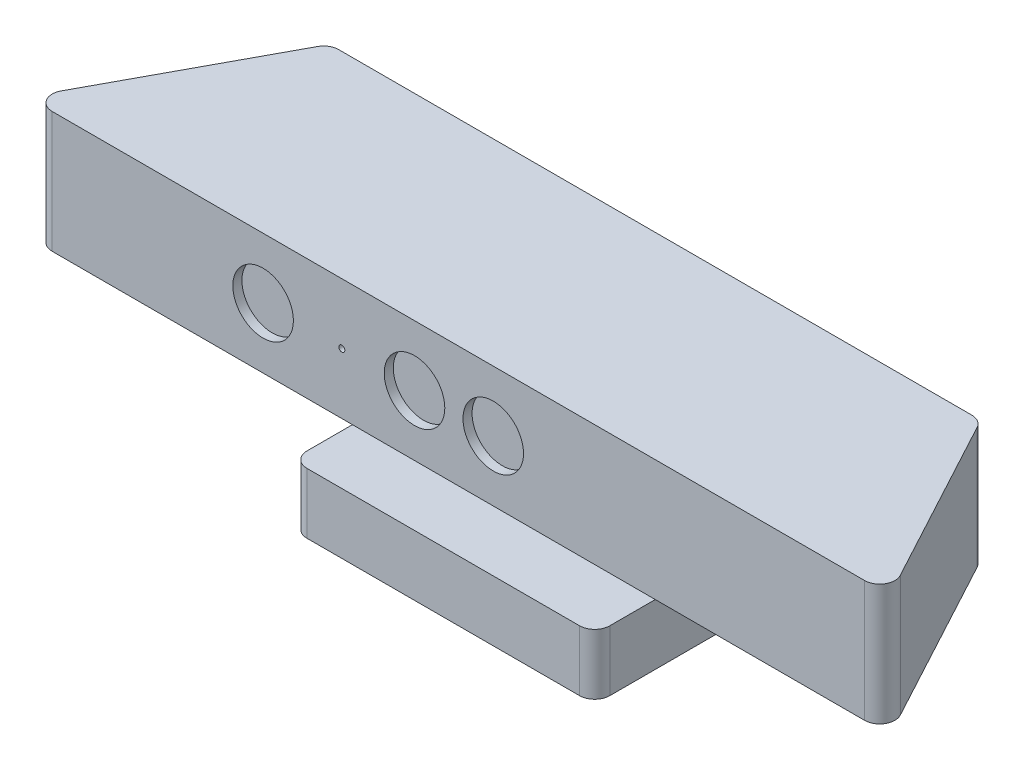
SolidWorks part; units mm, degrees
ref_plane "Front Plane" through (0, 0, 0) normal (0, 0, 1) x (1, 0, 0)
ref_plane "Top Plane" through (0, 0, 0) normal (0, 1, 0) x (1, 0, 0)
ref_plane "Right Plane" through (0, 0, 0) normal (1, 0, 0) x (0, 0, -1)
sketch "Sketch2" plane through (0, 0, 0) normal (0, 1, 0) x (1, 0, 0)
  line L0 (0, -15.7414) -> (0, -80.7414) construction
  line L2 (-107.5, -15.7414) -> (107.5, -15.7414)
  line L3 (-142.5, -80.7414) -> (142.5, -80.7414)
  line L4 (-142.5, -80.7414) -> (-107.5, -15.7414)
  line L5 (142.5, -80.7414) -> (107.5, -15.7414)
  line L6 (-125, -48.2414) -> (125, -48.2414) construction
  point P4 (0, 0)
  point P8 (0, 0)
  point P11 (0, -15.7414)
  point P14 (0, -80.7414)
  dimension "D1" = 215
  dimension "D2" = 285
  dimension "D3" = 65
extrude "Boss-Extrude1" add sketch "Sketch2" along normal blind 40 contours L4 L2 L5 L3
sketch "Sketch3" plane through (0, 0, 80.7414) normal (0, 0, 1) x (1, 0, 0)
  line L0 (-142.5, 0) -> (142.5, 0) construction
  line L1 (-142.5, 40) -> (-142.5, 0) construction
  circle A0 centre (-64.5, 20) radius 10
  circle A1 centre (-38.5, 20) radius 1
  circle A2 centre (-14.5, 20) radius 10
  circle A3 centre (11.5, 20) radius 10
  dimension "D1" = 20
  dimension "D2" = 20
  dimension "D4" = 104
  dimension "D6" = 2
  dimension "D7" = 128
  dimension "D9" = 20
  dimension "D10" = 20
  dimension "D3" = 78
  dimension "D5" = 20
  dimension "D8" = 20
  dimension "D11" = 154
  dimension "D12" = 20
extrude "Cut-Extrude1" cut sketch "Sketch3" against normal blind 3
sketch "Sketch8" plane through (0, 0, 0) normal (0, -1, 0) x (1, 0, 0)
  line L1 (-142.5, 80.7414) -> (142.5, 80.7414) construction
  line L2 (142.5, 80.7414) -> (107.5, 15.7414) construction
  circle A0 centre (0, 48.2414) radius 10
  point P2 (125, 48.2414)
  point P6 (0, 80.7414)
  dimension "D1" = 20
  dimension "D2" = 32.5
  dimension "D3" = 125
extrude "Boss-Extrude2" add sketch "Sketch8" along normal blind 15
sketch "Sketch9" plane through (0, -15, 0) normal (0, -1, 0) x (1, 0, 0)
  line L1 (-50, 85.7414) -> (50, 85.7414)
  line L2 (-50, 85.7414) -> (-50, 10.7414)
  line L3 (-50, 10.7414) -> (50, 10.7414)
  line L4 (50, 85.7414) -> (50, 10.7414)
  line L5 (-50, 85.7414) -> (50, 10.7414) construction
  line L6 (-50, 10.7414) -> (50, 85.7414) construction
  point P0 (0, 48.2414)
  dimension "D1" = 100
  dimension "D2" = 75
extrude "Boss-Extrude3" add sketch "Sketch9" along normal blind 20
fillet "Fillet2" radius 5 4 edges at (142.5, 20, 80.7414) (107.5, 20, 15.7414) (-107.5, 20, 15.7414) (-142.5, 20, 80.7414)
fillet "Fillet3" radius 5 4 edges at (50, -25, 10.7414) (50, -25, 85.7414) (-50, -25, 10.7414) (-50, -25, 85.7414)
